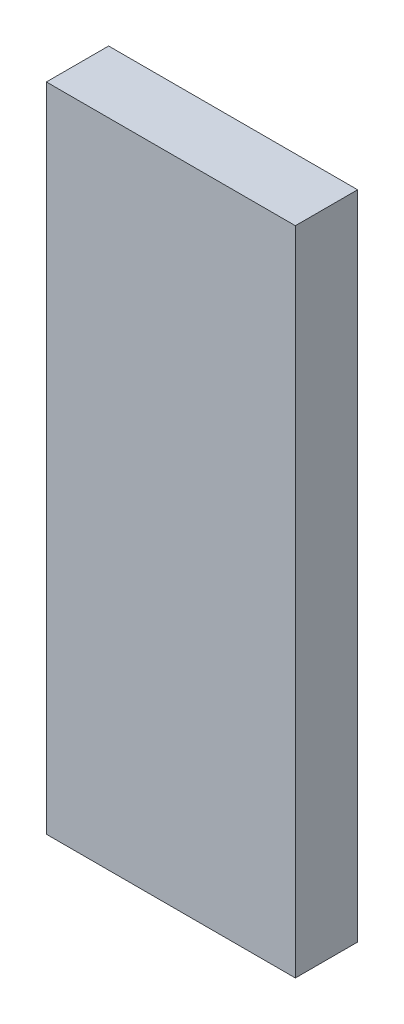
SolidWorks part; units mm, degrees
material "1.0037 (S235JR)"
ref_plane "Front Plane" through (0, 0, 0) normal (0, 0, 1) x (1, 0, 0)
ref_plane "Top Plane" through (0, 0, 0) normal (0, 1, 0) x (1, 0, 0)
ref_plane "Right Plane" through (0, 0, 0) normal (1, 0, 0) x (0, 0, -1)
sketch "Sketch1" plane through (0, 0, 0) normal (0, 0, 1) x (1, 0, 0)
  line L1 (0, 0) -> (60, 0)
  line L2 (0, 0) -> (0, 157)
  line L3 (0, 157) -> (60, 157)
  line L4 (60, 0) -> (60, 157)
  dimension "D1" = 157
  dimension "D2" = 60
extrude "Boss-Extrude1" add sketch "Sketch1" along normal blind 15
